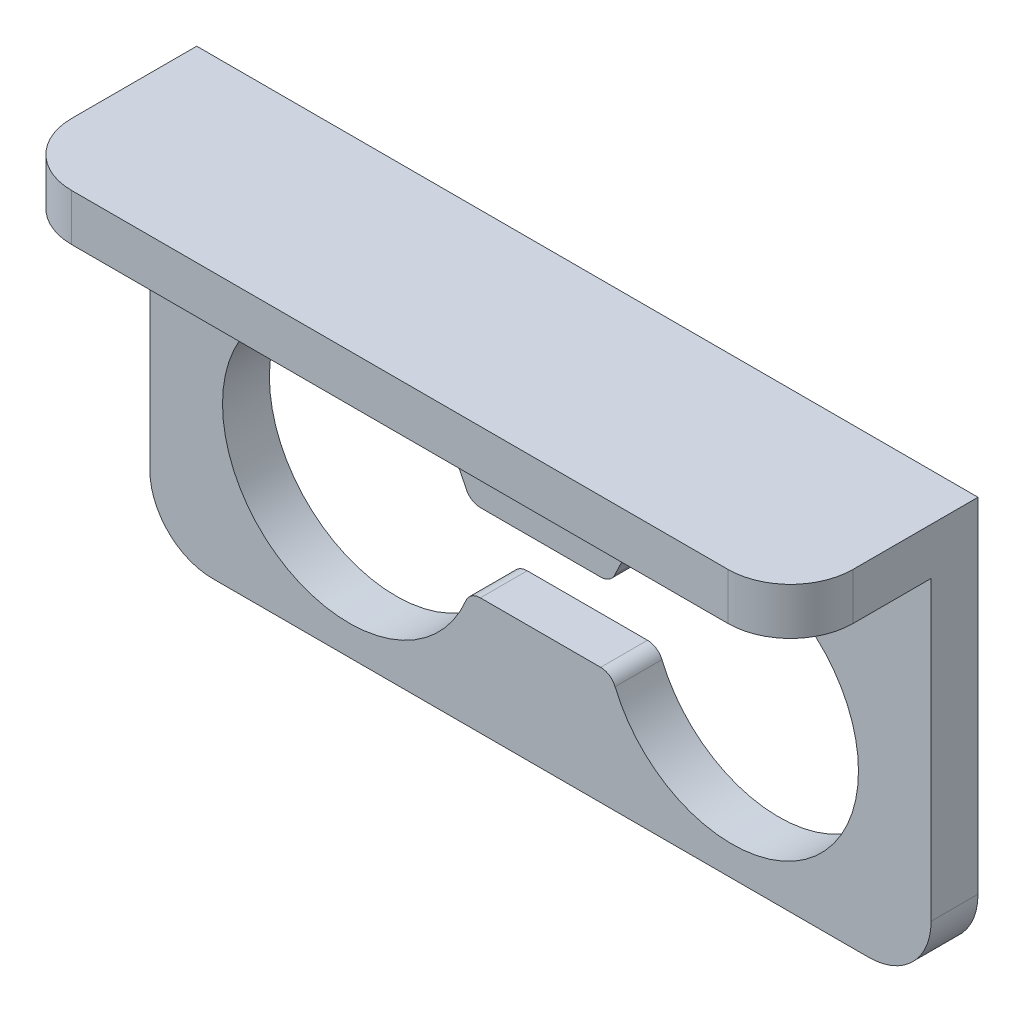
SolidWorks part; units mm, degrees
other "标注1"
sketch "草图6" plane through (25, -10, 15) normal (0.0929, -0.9273, 0.3626) x (0.5024, 0.3581, 0.787)
other "标注2"
sketch "草图7" plane through (25, -10, 15) normal (0.0929, -0.9273, 0.3626) x (0.5024, 0.3581, 0.787)
other "标注3"
sketch "草图8" plane through (25, -10, 15) normal (0.0929, -0.9273, 0.3626) x (0.5024, 0.3581, 0.787)
ref_plane "前视基准面" through (0, 0, 0) normal (0, 0, 1) x (1, 0, 0)
ref_plane "上视基准面" through (0, 0, 0) normal (0, 1, 0) x (1, 0, 0)
ref_plane "右视基准面" through (0, 0, 0) normal (1, 0, 0) x (0, 0, -1)
sketch "草图1" plane through (0, 0, 0) normal (0, 0, 1) x (1, 0, 0)
  line L1 (25, -10) -> (-25, -10)
  line L2 (25, -10) -> (25, 10)
  line L3 (25, 10) -> (-25, 10)
  line L4 (-25, -10) -> (-25, 10)
  line L5 (25, -10) -> (-25, 10) construction
  line L6 (25, 10) -> (-25, -10) construction
  line L8 (-3.85, 2.5) -> (3.85, 2.5)
  line L9 (3.85, -2.5) -> (-3.85, -2.5)
  line L10 (3.25, 7.25) -> (-3.25, 7.25) construction
  line L11 (3.25, 5.5) -> (-3.25, 5.5)
  line L12 (3.25, 9) -> (-3.25, 9)
  arc A7 (4.7731, -3.1154) -> (4.7731, 3.1154) centre (12.25, 0) ccw
  arc A8 (-4.7731, 3.1154) -> (-4.7731, -3.1154) centre (-12.25, 0) ccw
  arc A9 (3.85, -2.5) -> (4.7731, -3.1154) centre (3.85, -3.5) cw
  arc A10 (3.85, 2.5) -> (4.7731, 3.1154) centre (3.85, 3.5) ccw
  arc A11 (-3.85, -2.5) -> (-4.7731, -3.1154) centre (-3.85, -3.5) ccw
  arc A12 (-3.85, 2.5) -> (-4.7731, 3.1154) centre (-3.85, 3.5) cw
  arc A13 (3.25, 5.5) -> (3.25, 9) centre (3.25, 7.25) ccw
  arc A14 (-3.25, 9) -> (-3.25, 5.5) centre (-3.25, 7.25) ccw
  point P0 (0, 0)
  point P22 (0, 7.25)
  dimension "D3" = 1
  dimension "D4" = 8.1
  dimension "D5" = 8.1
  dimension "D6" = 2.5
  dimension "D8" = 12.25
  dimension "D9" = 12.25
  dimension "D12" = 1.75
  dimension "D1" = 20
  dimension "D2" = 50
  dimension "D7" = 2.5
  dimension "D10" = 7.25
  dimension "D11" = 6.5
  dimension "D13" = 3.25
extrude "凸台-拉伸1" add sketch "草图1" along normal blind 3
sketch "草图2" plane through (0, 10, 0) normal (0, 1, 0) x (1, 0, 0)
  line L1 (-25, 0) -> (25, 0)
  line L2 (-25, 0) -> (-25, -12)
  line L3 (-25, -12) -> (25, -12)
  line L4 (25, 0) -> (25, -12)
  dimension "D1" = 12
extrude "凸台-拉伸2" add sketch "草图2" along normal blind 6
sketch "草图5" plane through (0, 10, 0) normal (0, -1, 0) x (1, 0, 0)
  line L1 (25, 3) -> (-25, 3)
  line L2 (25, 3) -> (25, 12)
  line L3 (25, 12) -> (-25, 12)
  line L4 (-25, 3) -> (-25, 12)
extrude "切除-拉伸2" cut sketch "草图5" against normal blind 3
fillet "圆角1" radius 4 4 edges at (-25, 14.5, 12) (25, 14.5, 12) (25, -10, 1.5) (-25, -10, 1.5)
move or copy body "实体-移动/复制1" [suppressed] bodies to move or copy 118
